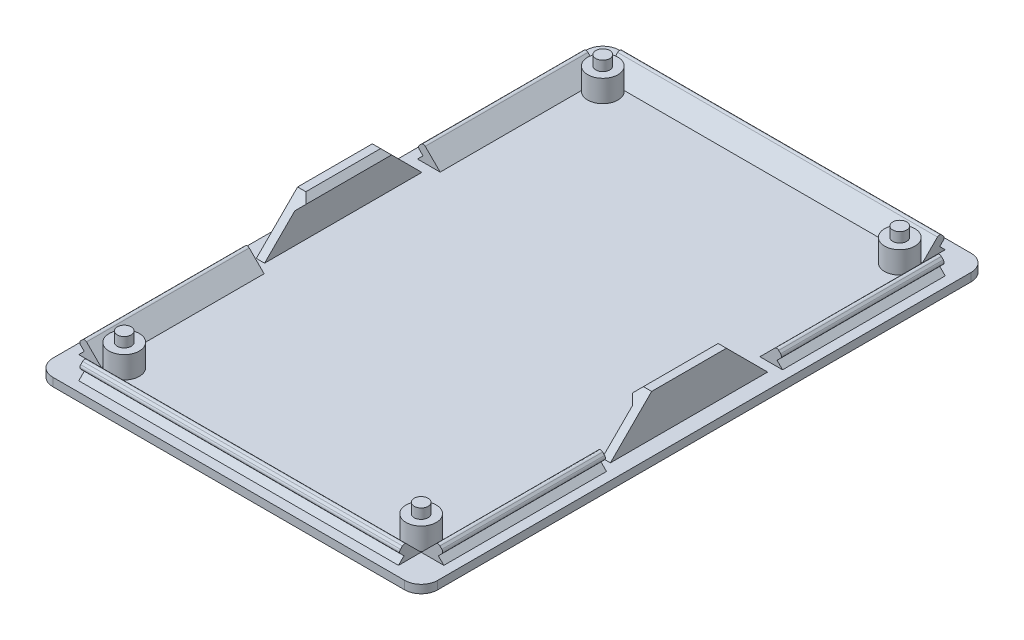
SolidWorks part; units mm, degrees
ref_plane "Front Plane" through (0, 0, 0) normal (0, 0, 1) x (1, 0, 0)
ref_plane "Top Plane" through (0, 0, 0) normal (0, 1, 0) x (1, 0, 0)
ref_plane "Right Plane" through (0, 0, 0) normal (1, 0, 0) x (0, 0, -1)
sketch "EDIT GLOBAL VARIABLE WITH PCB DIMENSIONS" plane through (0, 0, 0) normal (0, 1, 0) x (1, 0, 0)
  line L1 (-34.98, -51.49) -> (34.98, -51.49)
  line L2 (-34.98, -51.49) -> (-34.98, 51.49)
  line L3 (-34.98, 51.49) -> (34.98, 51.49)
  line L4 (34.98, -51.49) -> (34.98, 51.49)
  line L5 (-34.98, -51.49) -> (34.98, 51.49) construction
  line L6 (-34.98, 51.49) -> (34.98, -51.49) construction
  line L7 (-30.48, -46.99) -> (30.48, -46.99) construction
  line L8 (-30.48, -46.99) -> (-30.48, 46.99) construction
  line L9 (-30.48, 46.99) -> (30.48, 46.99) construction
  line L10 (30.48, -46.99) -> (30.48, 46.99) construction
  line L11 (-30.48, -46.99) -> (30.48, 46.99) construction
  line L12 (-30.48, 46.99) -> (30.48, -46.99) construction
  point P0 (0, 0)
  point P6 (0, 0)
  dimension "D3" = 4.5
  dimension "D4" = 4.5
  dimension "D1" = 93.98
  dimension "D2" = 60.96
extrude "Boss-Extrude1" add sketch "EDIT GLOBAL VARIABLE WITH PCB DIMENSIONS" along normal blind 1.5
fillet "Fillet1" radius 3 4 edges at (-34.98, 0.75, -51.49) (34.98, 0.75, -51.49) (34.98, 0.75, 51.49) (-34.98, 0.75, 51.49)
ref_plane "Plane1" through (-33.18, 0, 0) normal (-1, 0, 0) x (0, 0, 1)
ref_plane "Plane2" through (0, 0, 49.69) normal (0, 0, 1) x (1, 0, 0)
ref_plane "Plane3" through (33.18, 0, 0) normal (1, 0, 0) x (0, 0, -1)
ref_plane "Plane4" through (0, 0, -49.69) normal (0, 0, -1) x (-1, 0, 0)
ref_plane "Plane5" through (0, 0, -45.5687) normal (0, 0, -1) x (-1, 0, 0)
ref_plane "Plane6" through (-29.0587, 0, 0) normal (-1, 0, 0) x (0, 0, 1)
ref_plane "Plane7" through (0, 0, 45.5687) normal (0, 0, 1) x (1, 0, 0)
ref_plane "Plane8" through (29.0587, 0, 0) normal (1, 0, 0) x (0, 0, -1)
sketch "Sketch2" plane through (0, 0, 45.5687) normal (0, 0, 1) x (1, 0, 0)
  line L9 (33.18, 1.5) -> (29.0587, 1.5)
  line L11 (34.98, 1.5) -> (31.98, 1.5) construction
  line L12 (-31.98, 1.5) -> (31.98, 1.5) construction
  line L13 (29.0587, 1.5) -> (32.1193, 4.5607)
  line L14 (32.1193, 4.5607) -> (33.18, 3.5)
  line L15 (33.18, 3.5) -> (32.18, 2.5)
  line L16 (32.18, 2.5) -> (33.18, 1.5)
  line L17 (34.98, 1.5) -> (34.98, 0) construction
  line L18 (33.18, 3.5) -> (33.18, 1.5) construction
  dimension "D1" = 2
  dimension "D2" = 90
  dimension "D3" = 45
  dimension "D4" = 1.5
  dimension "D5" = 1.8
extrude "Boss-Extrude2" add sketch "Sketch2" against normal up to surface (91.1374 mm away) up to plane "Plane5"
sketch "Sketch3" plane through (0, 0, 45.5687) normal (0, 0, 1) x (1, 0, 0)
  line L9 (-33.18, 1.5) -> (-29.0587, 1.5)
  line L11 (-31.98, 1.5) -> (-34.98, 1.5) construction
  line L12 (-31.98, 1.5) -> (31.98, 1.5) construction
  line L13 (-29.0587, 1.5) -> (-32.1193, 4.5607)
  line L14 (-32.1193, 4.5607) -> (-33.18, 3.5)
  line L15 (-33.18, 3.5) -> (-32.18, 2.5)
  line L16 (-32.18, 2.5) -> (-33.18, 1.5)
  line L17 (-34.98, 0) -> (-34.98, 1.5) construction
  line L18 (-33.18, 3.5) -> (-33.18, 1.5) construction
  dimension "D1" = 45
  dimension "D2" = 90
  dimension "D3" = 1.5
  dimension "D4" = 2
  dimension "D5" = 1.8
extrude "Boss-Extrude3" add sketch "Sketch3" against normal up to surface (91.1374 mm away) up to plane "Plane5"
sketch "Sketch4" plane through (-29.0587, 0, 0) normal (-1, 0, 0) x (0, 0, 1)
  line L9 (-49.69, 1.5) -> (-45.5687, 1.5)
  line L12 (-48.49, 1.5) -> (-51.49, 1.5) construction
  line L13 (-48.49, 1.5) -> (48.49, 1.5) construction
  line L14 (-45.5687, 1.5) -> (-48.6293, 4.5607)
  line L15 (-48.6293, 4.5607) -> (-49.69, 3.5)
  line L16 (-49.69, 3.5) -> (-48.69, 2.5)
  line L17 (-48.69, 2.5) -> (-49.69, 1.5)
  line L18 (-51.49, 0) -> (-51.49, 1.5) construction
  dimension "D1" = 45
  dimension "D2" = 90
  dimension "D3" = 1.5
  dimension "D4" = 2
  dimension "D5" = 1.8
  dimension "D6" = 1.8
extrude "Boss-Extrude4" add sketch "Sketch4" against normal up to surface (58.1174 mm away) up to plane "Plane8"
sketch "Sketch5" plane through (-29.0587, 0, 0) normal (-1, 0, 0) x (0, 0, 1)
  line L0 (45.5687, 1.5) -> (49.69, 1.5)
  line L1 (-48.49, 1.5) -> (48.49, 1.5) construction
  line L2 (51.49, 1.5) -> (48.49, 1.5) construction
  line L3 (49.69, 1.5) -> (48.69, 2.5)
  line L4 (48.69, 2.5) -> (49.69, 3.5)
  line L5 (49.69, 3.5) -> (48.6293, 4.5607)
  line L6 (48.6293, 4.5607) -> (45.5687, 1.5)
  line L7 (51.49, 1.5) -> (51.49, 0) construction
  dimension "D1" = 45
  dimension "D2" = 90
  dimension "D3" = 1.5
  dimension "D4" = 90
  dimension "D5" = 1.8
  dimension "D6" = 1.8
  dimension "D7" = 2
extrude "Boss-Extrude5" add sketch "Sketch5" against normal up to surface (58.1174 mm away) up to plane "Plane8"
fillet "Fillet2" radius 0.5 8 edges at (0, 3.5, 49.69) (0, 4.5607, 48.6293) (-33.18, 3.5, 0) (-32.1193, 4.5607, 0) (0, 3.5, -49.69) (0, 4.5607, -48.6293) (33.18, 3.5, 0) (32.1193, 4.5607, 0)
sketch "Sketch7" plane through (0, 0, 0) normal (1, 0, 0) x (0, 0, -1)
  line L1 (45.5687, 1.5) -> (-45.5687, 1.5) construction
  line L2 (-16, 1.5) -> (-16, 4.3536)
  line L3 (45.5687, 4.3536) -> (-45.5687, 4.3536) construction
  line L4 (-16, 4.3536) -> (16, 4.3536)
  line L5 (16, 4.3536) -> (16, 1.5)
  line L6 (16, 1.5) -> (-16, 1.5)
  dimension "D1" = 32
  dimension "D2" = 16
extrude "Cut-Extrude1" cut sketch "Sketch7" against normal through all both and the other way through all
sketch "Sketch8" plane through (0, 1.5, 0) normal (0, 1, 0) x (1, 0, 0)
  line L0 (-34.98, 48.49) -> (-34.98, -48.49) construction
  line L1 (31.98, 51.49) -> (-31.98, 51.49) construction
  line L2 (34.98, -48.49) -> (34.98, 48.49) construction
  line L3 (-31.98, -51.49) -> (31.98, -51.49) construction
  circle A0 centre (-26.9873, 43.4973) radius 2.75
  circle A1 centre (26.9873, 43.4973) radius 2.75
  circle A2 centre (-26.9873, -43.4973) radius 2.75
  circle A3 centre (26.9873, -43.4973) radius 2.75
  dimension "D2" = 5.5
  dimension "D3" = 5.5
  dimension "D4" = 5.5
  dimension "D13" = 5.5
  dimension "D5" = 7.9927
  dimension "D6" = 7.9927
  dimension "D7" = 7.9927
  dimension "D8" = 7.9927
  dimension "D9" = 7.9927
  dimension "D10" = 7.9927
  dimension "D11" = 7.9927
  dimension "D12" = 7.9927
extrude "Boss-Extrude6" add sketch "Sketch8" along normal blind 4
sketch "Sketch10" plane through (0, 5.5, 0) normal (0, 1, 0) x (1, 0, 0)
  circle A0 centre (-26.9873, 43.4973) radius 1.27
  circle A1 centre (26.9873, 43.4973) radius 1.27
  circle A2 centre (26.9873, -43.4973) radius 1.27
  circle A3 centre (-26.9873, -43.4973) radius 1.27
  dimension "D1" = 2.54
  dimension "D2" = 2.54
  dimension "D3" = 2.54
  dimension "D4" = 2.54
sketch "Sketch11" plane through (0, 0, 0) normal (0, 0, 1) x (1, 0, 0)
  line L0 (-32.18, 1.5) -> (-32.18, 9.0002)
  line L1 (-31.98, 1.5) -> (-34.98, 1.5) construction
  line L2 (-32.18, 9.0002) -> (-30.68, 9.0002)
  line L3 (-30.68, 9.0002) -> (-30.68, 1.5)
  line L4 (-33.18, 1.5) -> (-29.0587, 1.5) construction
  line L5 (-30.68, 1.5) -> (-32.18, 1.5)
  line L6 (-34.98, 0) -> (-34.98, 1.5) construction
  line L7 (32.18, 1.5) -> (32.18, 9.0002)
  line L8 (34.98, 1.5) -> (31.98, 1.5) construction
  line L9 (30.68, 1.5) -> (30.68, 9.0002)
  line L10 (30.68, 9.0002) -> (32.18, 9.0002)
  line L11 (32.18, 1.5) -> (30.68, 1.5)
  line L12 (34.98, 1.5) -> (34.98, 0) construction
  dimension "D2" = 1.5
  dimension "D3" = 2.8
  dimension "D5" = 1.5
  dimension "D6" = 2.8
  dimension "D1" = 7.5002
  dimension "D4" = 7.5002
extrude "Boss-Extrude8" add sketch "Sketch11" along normal mid plane 28.5865
sketch "Sketch12" plane through (0, 0, 0) normal (0, 0, 1) x (1, 0, 0)
  line L0 (30.68, 9.0002) -> (30.68, 7.0002)
  line L1 (30.68, 9.0002) -> (30.68, 1.5) construction
  line L2 (30.68, 7.0002) -> (29.68, 8.0002)
  line L3 (29.68, 8.0002) -> (30.68, 9.0002)
  line L4 (-30.68, 9.0002) -> (-30.68, 7.0002)
  line L5 (-30.68, 1.5) -> (-30.68, 9.0002) construction
  line L6 (-30.68, 7.0002) -> (-29.68, 8.0002)
  line L7 (-29.68, 8.0002) -> (-30.68, 9.0002)
  dimension "D1" = 2
  dimension "D2" = 2
  dimension "D3" = 1.4142
  dimension "D4" = 1.4142
extrude "Boss-Extrude9" add sketch "Sketch12" along normal mid plane 28.5865
chamfer "Chamfer1" distance 7.5 angle 45 4 edges at (31.43, 9.0002, -14.2933) (31.43, 9.0002, 14.2933) (-31.43, 9.0002, -14.2933) (-31.43, 9.0002, 14.2933)
extrude "Boss-Extrude10" add sketch "Sketch10" along normal blind 1.8002
equation "\"LENGTH\"= 3.7in\t\t\t'longest of two dimensions of pcb"
equation "\"WIDTH\"= 2.4in\t\t\t'shortest of two dimensions of pcb"
equation "\"HOLE_DIA\"= 0.1in\t\t'mounting hole diameter"
equation "\"HOLE_DIST\"= .1375069in\t\t'distance to mount hole centerline from edge of PCB"
equation "\"PCB_THICK\"= 0.063in\t\t'nominal thickness of PCB, usually 1.6mm"
equation "\"TOP_CLEAR\"= 1in\t\t'Clearance above top of PCB, tallest component plus desired clearance"
equation "\"BOTTOM_CLEAR\"= 4mm\t\t'Clearance below bottom of PCB, minimum 4mm"
equation "\"D1@Sketch11\"=\"PCB_THICK\"+\"BOTTOM_CLEAR\"+1.9"
equation "\"D3@Sketch8\"=\"D2@Sketch8\""
equation "\"D4@Sketch8\"=\"D2@Sketch8\""
equation "\"D13@Sketch8\"=\"D2@Sketch8\""
equation "\"D1@Boss-Extrude6\"=\"BOTTOM_CLEAR\""
equation "\"D1@Sketch10\"=\"HOLE_DIA\""
equation "\"D2@Sketch10\"=\"D1@Sketch10\""
equation "\"D3@Sketch10\"=\"D1@Sketch10\""
equation "\"D4@Sketch10\"=\"D1@Sketch10\""
equation "\"D1@Boss-Extrude10\"=\"PCB_THICK\"+0.2mm"
equation "\"D4@Sketch11\"=\"D1@Sketch11\""
equation "\"D1@EDIT GLOBAL VARIABLE WITH PCB DIMENSIONS\"=\"LENGTH\""
equation "\"D2@EDIT GLOBAL VARIABLE WITH PCB DIMENSIONS\"=\"WIDTH\""
